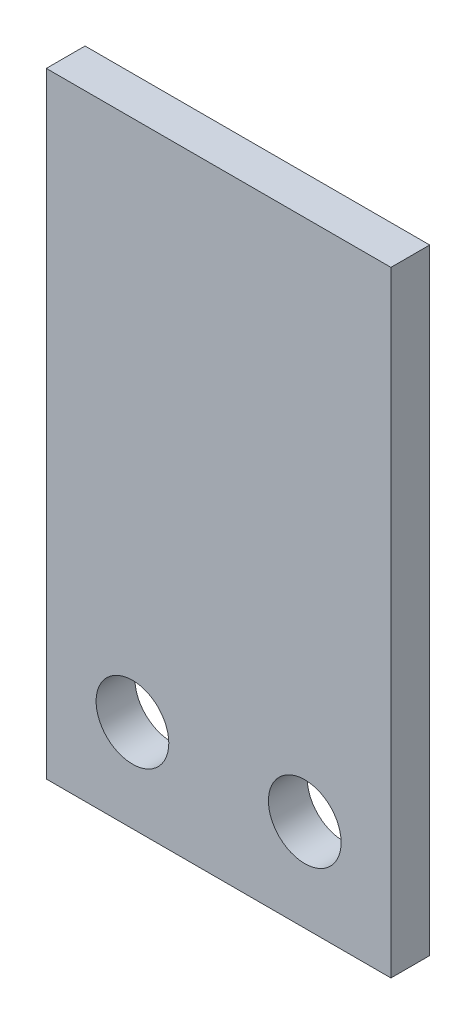
SolidWorks part; units mm, degrees
ref_plane "Front Plane" through (0, 0, 0) normal (0, 0, 1) x (1, 0, 0)
ref_plane "Top Plane" through (0, 0, 0) normal (0, 1, 0) x (1, 0, 0)
ref_plane "Right Plane" through (0, 0, 0) normal (1, 0, 0) x (0, 0, -1)
sketch "Sketch1" plane through (0, 0, 0) normal (0, 0, 1) x (1, 0, 0)
  line L0 (-1001.3028, -8.89) -> (48998.6972, -8.89) construction
  line L1 (-7.112, -12.7) -> (7.112, -12.7)
  line L2 (-7.112, -12.7) -> (-7.112, 12.7)
  line L3 (-7.112, 12.7) -> (7.112, 12.7)
  line L4 (7.112, -12.7) -> (7.112, 12.7)
  line L5 (-7.112, -12.7) -> (7.112, 12.7) construction
  line L6 (-7.112, 12.7) -> (7.112, -12.7) construction
  circle A0 centre (-3.556, -8.89) radius 1.5
  circle A1 centre (3.556, -8.89) radius 1.5
  point P0 (0, 0)
  dimension "D4" = 3
  dimension "D5" = 3
  dimension "D1" = 25.4
  dimension "D2" = 14.224
  dimension "D3" = 3.81
  dimension "D6" = 3.556
  dimension "D7" = 10.668
extrude "Boss-Extrude1" add sketch "Sketch1" along normal blind 1.6
